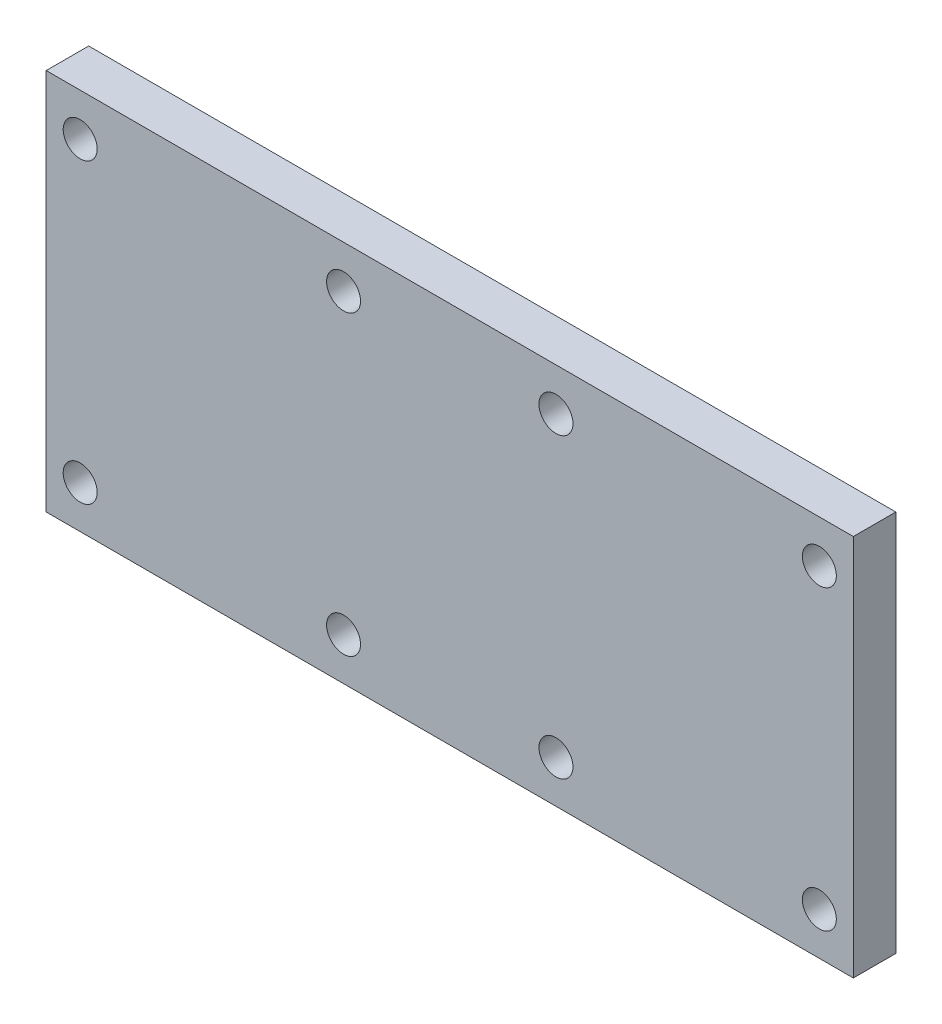
SolidWorks part; units mm, degrees
ref_plane "Front Plane" through (0, 0, 0) normal (0, 0, 1) x (1, 0, 0)
ref_plane "Top Plane" through (0, 0, 0) normal (0, 1, 0) x (1, 0, 0)
ref_plane "Right Plane" through (0, 0, 0) normal (1, 0, 0) x (0, 0, -1)
sketch "Sketch1" plane through (0, 0, 0) normal (0, 0, 1) x (1, 0, 0)
  line L1 (-47.5, 22.5) -> (47.5, 22.5)
  line L2 (-47.5, 22.5) -> (-47.5, -22.5)
  line L3 (-47.5, -22.5) -> (47.5, -22.5)
  line L4 (47.5, 22.5) -> (47.5, -22.5)
  line L5 (-47.5, 22.5) -> (47.5, -22.5) construction
  line L6 (-47.5, -22.5) -> (47.5, 22.5) construction
  point P0 (0, 0)
  dimension "D1" = 45
  dimension "D2" = 95
extrude "Boss-Extrude1" add sketch "Sketch1" along normal blind 5
sketch "Sketch2" plane through (0, 0, 5) normal (0, 0, 1) x (1, 0, 0)
  circle A0 centre (43.5, 17.5) radius 2
  circle A1 centre (43.5, -17.5) radius 2
  circle A2 centre (12.5, -17.5) radius 2
  circle A3 centre (12.5, 17.5) radius 2
  circle A4 centre (-12.5, 17.5) radius 2
  circle A5 centre (-12.5, -17.5) radius 2
  circle A6 centre (-43.5, -17.5) radius 2
  circle A7 centre (-43.5, 17.5) radius 2
extrude "Cut-Extrude1" cut sketch "Sketch2" against normal through all
